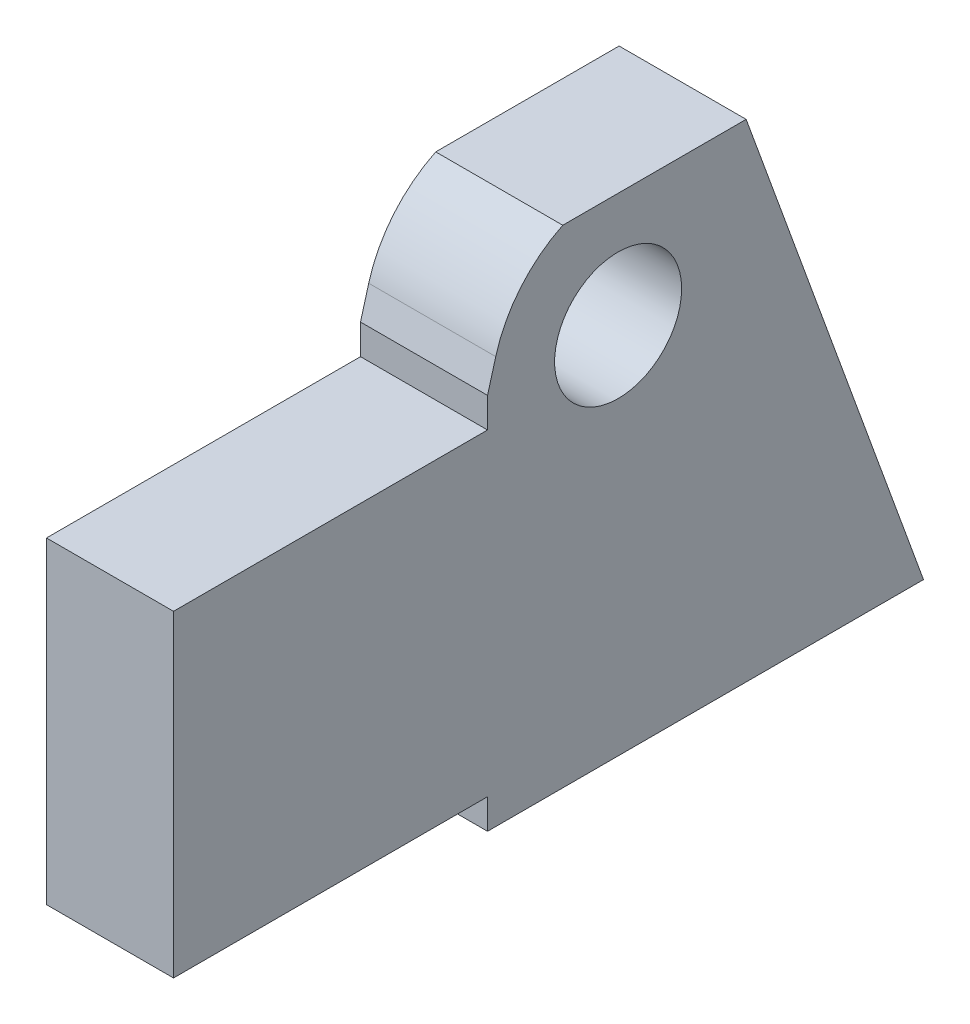
SolidWorks part; units mm, degrees
material "Alum Plate"
ref_plane "Front Plane" through (0, 0, 0) normal (0, 0, 1) x (1, 0, 0)
ref_plane "Top Plane" through (0, 0, 0) normal (0, 1, 0) x (1, 0, 0)
ref_plane "Right Plane" through (0, 0, 0) normal (1, 0, 0) x (0, 0, -1)
other "Bounding Box"
ref_plane "Default Plane" through (-8.9266, -12.7485, 0) normal (-0.1736, 0.9848, 0) x (0.9848, 0.1736, 0)
sketch "Sketch2" plane through (0, 0, 0) normal (1, 0, 0) x (0, 0, -1)
  line L6 (0, 31.75) -> (0, 0)
  line L8 (0, 31.75) -> (31.3944, 31.75)
  line L10 (31.3944, 0) -> (0, 0)
  line L11 (31.3944, 0) -> (31.3944, 31.75) construction
  line L12 (31.3944, 31.75) -> (31.3944, 34.7472)
  line L13 (31.3944, 34.7472) -> (61.243, 34.7472)
  line L14 (61.243, 34.7472) -> (74.9808, -2.9972)
  line L15 (31.3944, 0) -> (31.3944, -2.9972)
  line L16 (31.3944, -2.9972) -> (74.9808, -2.9972)
  dimension "D1" = 31.3944
  dimension "D2" = 31.75
  dimension "D3" = 74.9808
  dimension "D7" = 2.9972
  dimension "D8" = 70
extrude "Boss-Extrude1" add sketch "Sketch2" along normal mid plane 12.7
sketch "Sketch4" plane through (6.35, 0, 0) normal (1, 0, 0) x (0, 0, -1)
  line L0 (57.1418, 34.7472) -> (61.243, 34.7472)
  line L1 (0, 31.75) -> (0, 0) construction
  line L2 (31.3944, 34.7472) -> (32.2152, 37.6958)
  line L3 (31.3944, 34.7472) -> (31.7582, 34.7472)
  line L4 (61.243, 34.7472) -> (31.3944, 34.7472) construction
  line L6 (61.243, 34.7472) -> (57.2492, 45.72)
  line L7 (57.2492, 45.72) -> (38.9142, 45.72)
  line L8 (74.9808, -2.9972) -> (61.243, 34.7472) construction
  line L9 (0, 0) -> (31.3944, 0) construction
  arc A0 (31.7582, 34.7472) -> (57.1418, 34.7472) centre (44.45, 34.29) ccw
  arc A1 (38.9142, 45.72) -> (32.2152, 37.6958) centre (44.45, 34.29) ccw
  dimension "D3" = 25.4
  dimension "D1" = 34.29
  dimension "D2" = 44.45
  dimension "D4" = 11.43
extrude "Boss-Extrude2" add sketch "Sketch4" against normal through all
sketch "Sketch5" plane through (6.35, 0, 0) normal (1, 0, 0) x (0, 0, -1)
  circle A0 centre (44.45, 34.29) radius 6.35
  arc A3 (38.9142, 45.72) -> (32.2152, 37.6958) centre (44.45, 34.29) ccw construction
  dimension "D1" = 12.7
extrude "Cut-Extrude2" cut sketch "Sketch5" against normal through all
